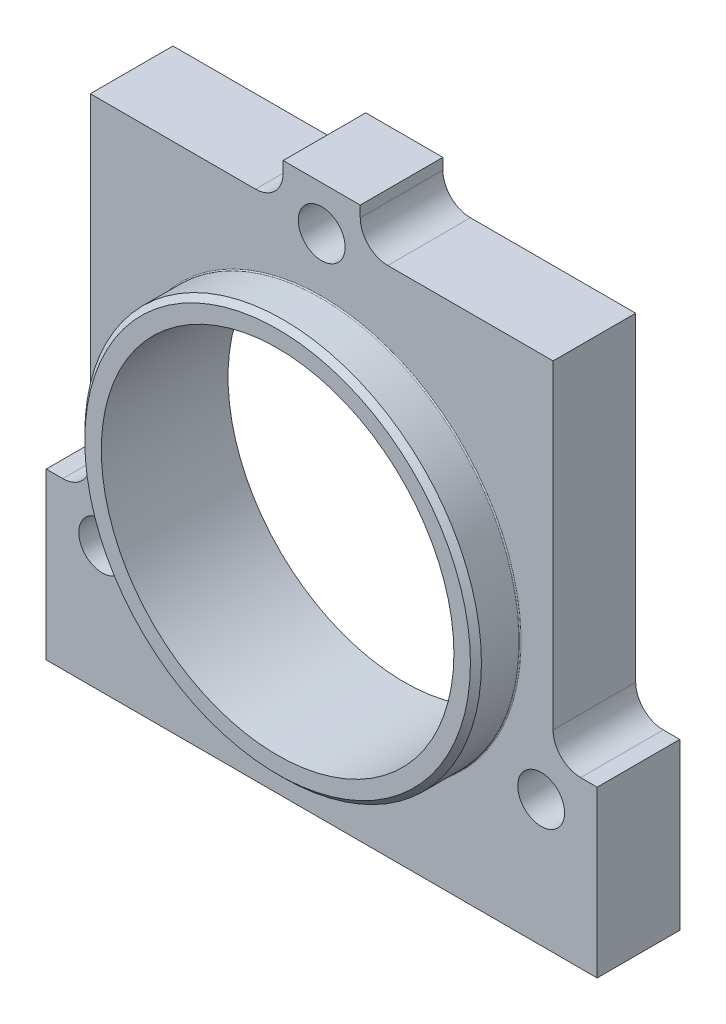
SolidWorks part; units mm, degrees
material "3.1325 (EN-AW 2017A)"
ref_plane "Plan de face" through (0, 0, 0) normal (0, 0, 1) x (1, 0, 0)
ref_plane "Plan de dessus" through (0, 0, 0) normal (0, 1, 0) x (1, 0, 0)
ref_plane "Plan de droite" through (0, 0, 0) normal (1, 0, 0) x (0, 0, -1)
sketch "Esquisse1" plane through (0, 0, 0) normal (0, 0, 1) x (1, 0, 0)
  line L0 (0, 72.7397) -> (0, -96.9863) construction
  line L1 (-71.2182, 0) -> (96.3994, 0) construction
  line L2 (-7, 54) -> (7, 54)
  line L3 (7, 54) -> (7, 52)
  line L4 (12, 47) -> (42, 47)
  line L5 (42, 47) -> (42, -11)
  line L6 (47, -16) -> (50, -16)
  line L7 (50, -16) -> (50, -46)
  line L8 (50, -46) -> (-50, -46)
  line L9 (-50, -46) -> (-50, -16)
  line L10 (-50, -16) -> (-47, -16)
  line L11 (-42, -11) -> (-42, 47)
  line L12 (-42, 47) -> (-12, 47)
  line L13 (-7, 52) -> (-7, 54)
  circle A0 centre (0, 0) radius 32
  arc A1 (-47, -16) -> (-42, -11) centre (-47, -11) ccw
  arc A2 (42, -11) -> (47, -16) centre (47, -11) ccw
  arc A3 (12, 47) -> (7, 52) centre (12, 52) cw
  arc A4 (-12, 47) -> (-7, 52) centre (-12, 52) ccw
  point P25 (7, 47)
  dimension "D1" = 64
  dimension "D12" = 5
  dimension "D2" = 46
  dimension "D3" = 100
  dimension "D4" = 50
  dimension "D5" = 54
  dimension "D6" = 42
  dimension "D7" = 42
  dimension "D8" = 35
  dimension "D9" = 35
  dimension "D10" = 30
  dimension "D11" = 63
extrude "Boss.-Extru.1" add sketch "Esquisse1" along normal blind 15
sketch "Esquisse2" plane through (0, 0, 15) normal (0, 0, 1) x (1, 0, 0)
  circle A0 centre (0, 0) radius 32
  circle A1 centre (0, 0) radius 36
  circle A2 centre (0, 0) radius 32 construction
  dimension "D1" = 72
extrude "Boss.-Extru.2" add sketch "Esquisse2" along normal blind 8
chamfer "Chanfrein1" distance 1 angle 45 1 edges at (36, 0, 23)
fillet "Congé1" radius 0.2 1 edges at (-36, 0, 15)
sketch "Esquisse3" plane through (0, 0, 0) normal (0, 0, -1) x (-1, 0, 0)
  circle A0 centre (0, 0) radius 46 construction
  circle A1 centre (0, 46) radius 4.25
  dimension "D1" = 92
  dimension "D2" = 8.5
extrude "Enlèv. mat.-Extru.1" cut sketch "Esquisse3" against normal through all
sketch "Esquisse4" plane through (0, 0, 0) normal (0, 0, -1) x (-1, 0, 0)
  circle A0 centre (0, 46) radius 7
  dimension "D1" = 14
extrude "Enlèv. mat.-Extru.2" cut sketch "Esquisse4" against normal blind 8
pattern_circular "Répétition circulaire1" count 3 over 360 about axis through (0, 0, 0) along (0, 0, 1) of "Enlèv. mat.-Extru.1", "Enlèv. mat.-Extru.2"
